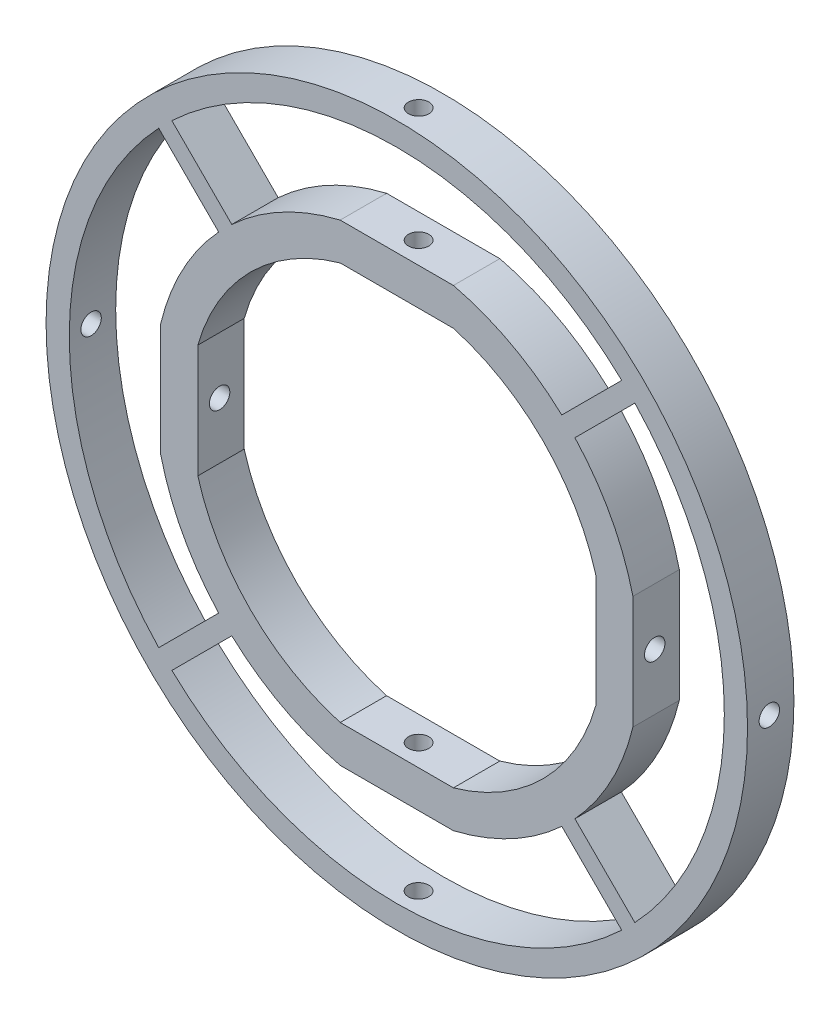
SolidWorks part; units mm, degrees
ref_plane "Front Plane" through (0, 0, 0) normal (0, 0, 1) x (1, 0, 0)
ref_plane "Top Plane" through (0, 0, 0) normal (0, 1, 0) x (1, 0, 0)
ref_plane "Right Plane" through (0, 0, 0) normal (1, 0, 0) x (0, 0, -1)
sketch "Sketch1" plane through (0, 0, 0) normal (0, 0, 1) x (1, 0, 0)
  line L0 (-6.1, 25.44) -> (6.1, 25.44)
  line L1 (0, 0) -> (-25.44, 0) construction
  line L2 (-25.44, -6.1) -> (-25.44, 6.1)
  line L18 (-6.1, 25.44) -> (-6.1, 21.44)
  line L19 (-6.1, 21.44) -> (6.1, 21.44)
  line L20 (6.1, 25.44) -> (6.1, 21.44)
  line L21 (-25.44, -6.1) -> (-21.44, -6.1)
  line L22 (-25.44, -6.1) -> (-25.44, 6.1)
  line L23 (-25.44, 6.1) -> (-21.44, 6.1)
  line L24 (-21.44, -6.1) -> (-21.44, 6.1)
  line L25 (25.44, 6.1) -> (25.44, -6.1)
  line L26 (25.44, 6.1) -> (21.44, 6.1)
  line L27 (21.44, 6.1) -> (21.44, -6.1)
  line L28 (25.44, -6.1) -> (21.44, -6.1)
  line L29 (6.1, -25.44) -> (-6.1, -25.44)
  line L30 (6.1, -25.44) -> (6.1, -21.44)
  line L31 (6.1, -21.44) -> (-6.1, -21.44)
  line L32 (-6.1, -25.44) -> (-6.1, -21.44)
  arc A0 (-21.44, 6.1) -> (-6.1, 21.44) centre (0, 0) cw
  arc A1 (-25.44, 6.1) -> (-6.1, 25.44) centre (0, 0) cw
  arc A2 (6.1, 25.44) -> (25.44, 6.1) centre (0, 0) cw
  arc A3 (6.1, 21.44) -> (21.44, 6.1) centre (0, 0) cw
  arc A4 (25.44, -6.1) -> (6.1, -25.44) centre (0, 0) cw
  arc A5 (21.44, -6.1) -> (6.1, -21.44) centre (0, 0) cw
  arc A6 (-6.1, -25.44) -> (-25.44, -6.1) centre (0, 0) cw
  arc A7 (-6.1, -21.44) -> (-21.44, -6.1) centre (0, 0) cw
  point P6 (-25.44, 0)
  point P22 (0, 0)
  point P24 (0, 0)
  point P39 (0, 0)
  point P41 (0, 0)
  dimension "D1" = 25.44
  dimension "D2" = 12.2
  dimension "D3" = 4
  dimension "D6" = 4
  dimension "D4" = 4
extrude "Boss-Extrude1" add sketch "Sketch1" along normal blind 5
sketch "Sketch3" plane through (0, 25.44, 0) normal (0, 1, 0) x (1, 0, 0)
  line L0 (0, 0) -> (0, -2.65) construction
  circle A0 centre (0, -2.65) radius 1.1
  dimension "D2" = 2.2
  dimension "D1" = 2.65
extrude "Cut-Extrude2" cut sketch "Sketch3" against normal up to surface (4 mm away) and the other way through all up to face at (0, 21.44, 2.5)
pattern_circular "CirPattern7" count 4 over 360 about axis through (0, 0, 5) along (0, 0, -1) of "Cut-Extrude2"
sketch "Sketch4" plane through (0, 0, 5) normal (0, 0, 1) x (1, 0, 0)
  line L0 (-18.4987, 18.4987) -> (-24.9538, 24.9538) construction
  line L1 (-19.1923, 17.7781) -> (-25.6509, 24.2367)
  line L2 (-17.7781, 19.1923) -> (-24.2367, 25.6509)
  line L3 (-19.2058, 17.7916) -> (-25.6609, 24.2467) construction
  line L4 (-17.7916, 19.2058) -> (-24.2467, 25.6609) construction
  line L5 (17.7781, 19.1923) -> (24.2367, 25.6509)
  line L6 (19.1923, 17.7781) -> (25.6509, 24.2367)
  line L7 (19.1923, -17.7781) -> (25.6509, -24.2367)
  line L8 (17.7781, -19.1923) -> (24.2367, -25.6509)
  line L9 (-17.7781, -19.1923) -> (-24.2367, -25.6509)
  line L10 (-19.1923, -17.7781) -> (-25.6509, -24.2367)
  circle A21 centre (0, 0) radius 37.79
  arc A22 (-25.6509, 24.2367) -> (-25.6509, -24.2367) centre (0, 0) ccw
  arc A23 (-6.1, 25.44) -> (-25.44, 6.1) centre (0, 0) ccw construction
  arc A24 (-17.7781, 19.1923) -> (-19.1923, 17.7781) centre (0, 0) ccw
  circle A25 centre (0, 0) radius 35.29 construction
  arc A26 (19.1923, 17.7781) -> (17.7781, 19.1923) centre (0, 0) ccw
  arc A27 (17.7781, -19.1923) -> (19.1923, -17.7781) centre (0, 0) ccw
  arc A28 (-19.1923, -17.7781) -> (-17.7781, -19.1923) centre (0, 0) ccw
  arc A29 (-24.2367, -25.6509) -> (24.2367, -25.6509) centre (0, 0) ccw
  arc A30 (25.6509, -24.2367) -> (25.6509, 24.2367) centre (0, 0) ccw
  arc A31 (24.2367, 25.6509) -> (-24.2367, 25.6509) centre (0, 0) ccw
  point P32 (0, 0)
  arc M18 (-25.44, -6.1) -> (-6.1, -25.44) centre (0, 0) ccw
  arc M20 (6.1, -25.44) -> (25.44, -6.1) centre (0, 0) ccw
  arc M22 (25.44, 6.1) -> (6.1, 25.44) centre (0, 0) ccw
  arc M24 (-6.1, 25.44) -> (-25.44, 6.1) centre (0, 0) ccw
  dimension "D1" = 75.58
  dimension "D2" = 2.5
  dimension "D5" = 4
  dimension "D3" = 1
  dimension "D4" = 1
extrude "Boss-Extrude2" add sketch "Sketch4" against normal up to surface (5 mm away) contours A21 A31 L5 L6 A30 L7 L8 A29 L9 L10 A22 L1 L2 M22 M20 M18 M24
sketch "Sketch5" plane through (-25.44, 0, 0) normal (-1, 0, 0) x (0, 0, 1)
  circle A0 centre (2.65, 0) radius 1.1
extrude "Cut-Extrude3" cut sketch "Sketch5" along normal through all
pattern_circular "CirPattern8" count 4 over 360 about axis through (0, 0, -106.8863) along (0, 0, 1) of "Cut-Extrude3"
